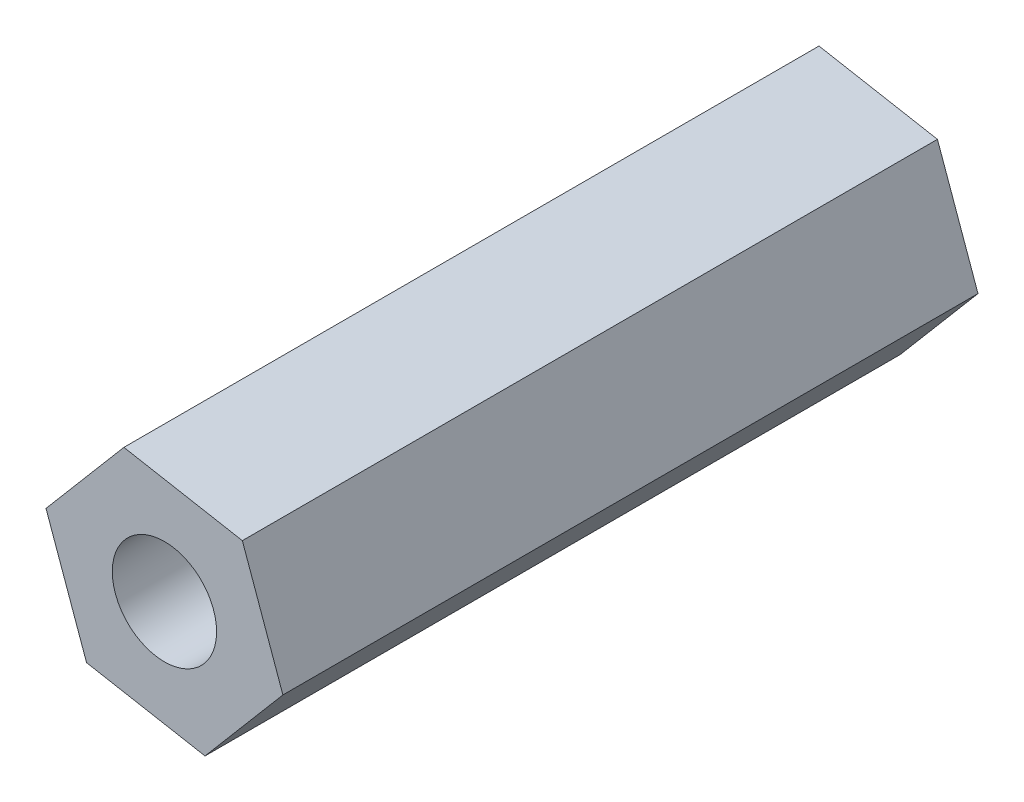
SolidWorks part; units mm, degrees
material "ABS"
ref_plane "Plano frontal" through (0, 0, 0) normal (0, 0, 1) x (1, 0, 0)
ref_plane "Plano superior" through (0, 0, 0) normal (0, 1, 0) x (1, 0, 0)
ref_plane "Plano direito" through (0, 0, 0) normal (1, 0, 0) x (0, 0, -1)
sketch "Esboço1" plane through (0, 0, 0) normal (0, 0, 1) x (1, 0, 0)
  line L1 (12.9332, -4.1439) -> (9.5251, -3.5237)
  line L2 (9.5251, -3.5237) -> (7.2839, -6.1651)
  line L3 (7.2839, -6.1651) -> (8.4508, -9.4267)
  line L4 (8.4508, -9.4267) -> (11.8589, -10.0469)
  line L5 (11.8589, -10.0469) -> (14.1001, -7.4055)
  line L6 (14.1001, -7.4055) -> (12.9332, -4.1439)
  circle A0 centre (10.692, -6.7853) radius 3 construction
extrude "Ressalto-extrusão1" add sketch "Esboço1" along normal blind 20
sketch "Esboço4" plane through (0, 0, 0) normal (0, 0, -1) x (-1, 0, 0)
  line L1 (-12.9332, -4.1439) -> (-9.5251, -3.5237) construction
  circle A0 centre (-10.692, -6.7853) radius 1.5
  dimension "D1" = 3
extrude "Corte-extrusão2" cut sketch "Esboço4" against normal blind 40
